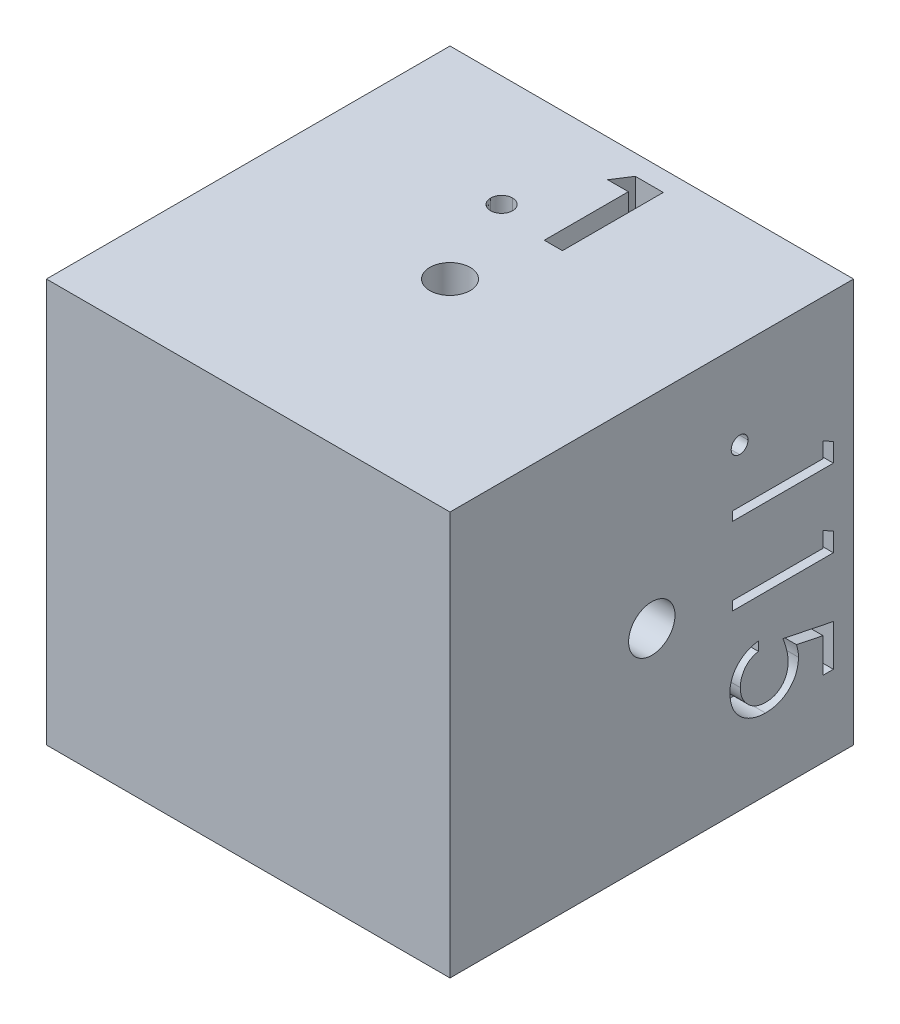
SolidWorks part; units mm, degrees
material "PLA/ABS"
ref_plane "Front Plane" through (0, 0, 0) normal (0, 0, 1) x (1, 0, 0)
ref_plane "Top Plane" through (0, 0, 0) normal (0, 1, 0) x (1, 0, 0)
ref_plane "Right Plane" through (0, 0, 0) normal (1, 0, 0) x (0, 0, -1)
other "Bounding Box"
ref_plane "Default Plane" through (13.8565, 3.175, 6.7999) normal (0, -1, 0) x (-1, 0, 0)
sketch "Sketch1" plane through (0, 0, 0) normal (0, 1, 0) x (1, 0, 0)
  line L1 (-12.7, -12.7) -> (12.7, -12.7)
  line L2 (-12.7, -12.7) -> (-12.7, 12.7)
  line L3 (-12.7, 12.7) -> (12.7, 12.7)
  line L4 (12.7, -12.7) -> (12.7, 12.7)
  line L5 (-12.7, -12.7) -> (12.7, 12.7) construction
  line L6 (-12.7, 12.7) -> (12.7, -12.7) construction
  point P0 (0, 0)
  dimension "D1" = 25.4
extrude "Boss-Extrude1" add sketch "Sketch1" along normal mid plane 25.4
sketch "Sketch2" plane through (0, 12.7, 0) normal (0, 1, 0) x (1, 0, 0)
  circle A0 centre (0, 0) radius 1.27
  point P0 (0, 0)
  point P9 (12.7, -8.9674)
  point P10 (0.5876, 0)
  dimension "D1" = 2.54
extrude "Cut-Extrude1" cut sketch "Sketch2" against normal blind 12.7
sketch "Sketch4" plane through (12.7, 0, 0) normal (1, 0, 0) x (0, 0, -1)
  circle A0 centre (0, 0) radius 1.4605
  dimension "D1" = 2.921
extrude "Cut-Extrude2" cut sketch "Sketch4" against normal blind 12.7
sketch "Sketch5" plane through (0, -12.7, 0) normal (0, -1, 0) x (1, 0, 0)
  circle A0 centre (0, 0) radius 1.524
  dimension "D1" = 3.048
extrude "Cut-Extrude3" cut sketch "Sketch5" against normal blind 12.7
sketch "Sketch6" plane through (-12.7, 0, 0) normal (1, 0, 0) x (0, 0, -1)
  circle A0 centre (0, 0) radius 1.5875
  dimension "D1" = 3.175
extrude "Cut-Extrude4" cut sketch "Sketch6" along normal blind 12.7
sketch "Sketch7" plane through (0, 12.7, 0) normal (0, 1, 0) x (1, 0, 0)
  line L0 (-12.7, 5.08) -> (12.7, 5.08) construction
  line L1 (-12.7, 12.7) -> (-12.7, -12.7) construction
  line L2 (12.7, -12.7) -> (12.7, 12.7) construction
  line L3 (12.7, 12.7) -> (-12.7, 12.7) construction
  text T0 "<b>.1</b>\r\n" font "Century Gothic" height 6.35
  dimension "D1" = 7.62
extrude "Cut-Extrude5" cut sketch "Sketch7" against normal blind 1.905
sketch "Sketch9" plane through (12.7, 0, 0) normal (1, 0, 0) x (0, 0, -1)
  line L0 (5.08, 12.7) -> (5.08, -12.7) construction
  line L1 (-12.7, 12.7) -> (12.7, 12.7) construction
  line L2 (-12.7, -12.7) -> (12.7, -12.7) construction
  text T0 ".115" font "Century Gothic" height 6.35
  point P6 (5.08, 12.7)
sketch "Sketch10" plane through (0, -12.7, 0) normal (0, -1, 0) x (-1, 0, 0)
  line L0 (-12.7, 5.08) -> (12.7, 5.08) construction
  line L1 (12.7, 12.7) -> (12.7, -12.7) construction
  text T0 ".12" font "Century Gothic" height 6.35
extrude "Cut-Extrude6" cut sketch "Sketch9" against normal blind 1.905
extrude "Cut-Extrude7" cut sketch "Sketch10" against normal blind 1.905
sketch "Sketch11" plane through (-12.7, 0, 0) normal (-1, 0, 0) x (0, 0, 1)
  line L0 (-5.08, -12.7) -> (-5.08, 12.7) construction
  line L2 (-12.7, -12.7) -> (12.7, -12.7) construction
  text T0 ".125" font "Century Gothic" height 6.35
  point P3 (-12.0251, -34.1751)
  point P4 (-5.08, 12.7)
  point P6 (-5.08, -12.7)
  point P10 (-2.9629, -12.7)
  point P11 (-6.3726, -12.7)
extrude "Cut-Extrude8" cut sketch "Sketch11" against normal blind 1.905
